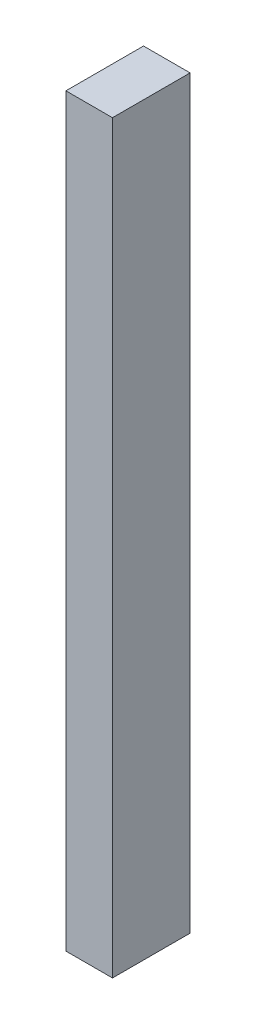
SolidWorks part; units mm, degrees
ref_plane "Front Plane" through (0, 0, 0) normal (0, 0, 1) x (1, 0, 0)
ref_plane "Top Plane" through (0, 0, 0) normal (0, 1, 0) x (1, 0, 0)
ref_plane "Right Plane" through (0, 0, 0) normal (1, 0, 0) x (0, 0, -1)
sketch "Sketch1" plane through (0, 0, 0) normal (0, 1, 0) x (1, 0, 0)
  line L1 (-19.05, -31.75) -> (19.05, -31.75)
  line L2 (-19.05, -31.75) -> (-19.05, 31.75)
  line L3 (-19.05, 31.75) -> (19.05, 31.75)
  line L4 (19.05, -31.75) -> (19.05, 31.75)
  line L5 (-19.05, -31.75) -> (19.05, 31.75) construction
  line L6 (-19.05, 31.75) -> (19.05, -31.75) construction
  point P0 (0, 0)
  dimension "D1" = 63.5
  dimension "D2" = 38.1
extrude "Boss-Extrude1" add sketch "Sketch1" along normal blind 609.6
